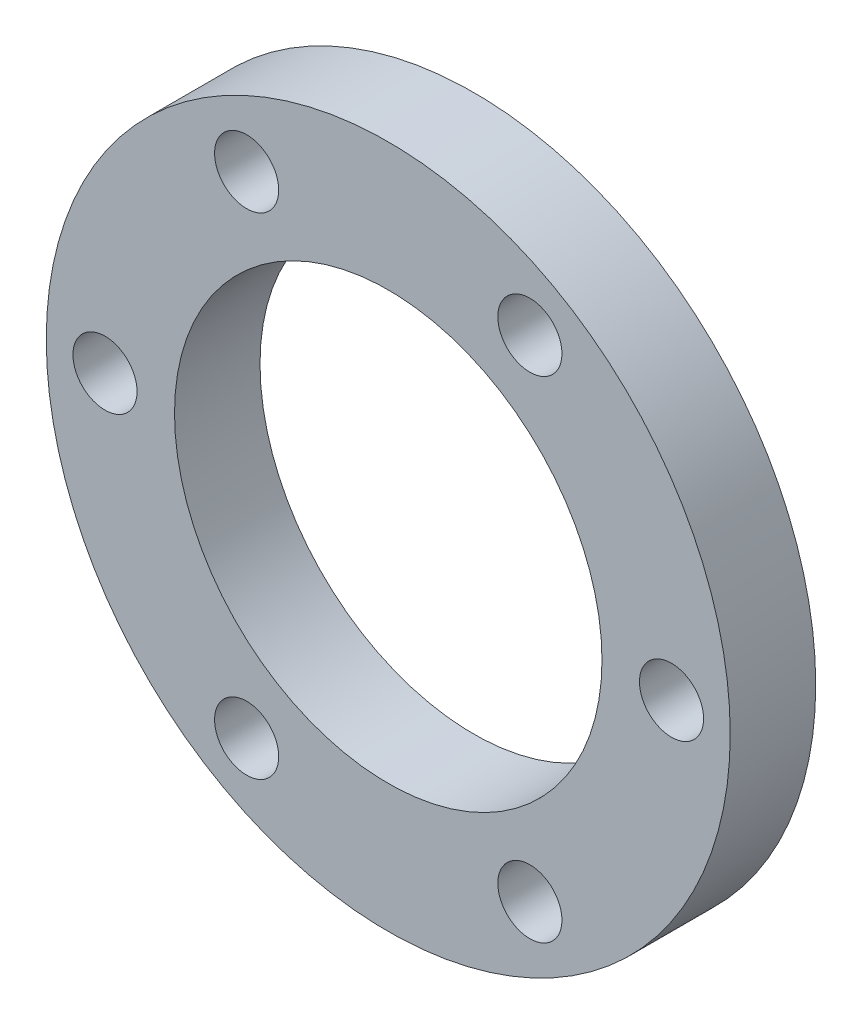
SolidWorks part; units mm, degrees
ref_plane "Front Plane" through (0, 0, 0) normal (0, 0, 1) x (1, 0, 0)
ref_plane "Top Plane" through (0, 0, 0) normal (0, 1, 0) x (1, 0, 0)
ref_plane "Right Plane" through (0, 0, 0) normal (1, 0, 0) x (0, 0, -1)
sketch "Sketch2" plane through (0, 0, 0) normal (0, 0, 1) x (1, 0, 0)
  line L0 (-99.7108, 0.0135) -> (108.6604, 0.0135) construction
  line L1 (0, 0) -> (-66.2605, 0) construction
  line L2 (0, 0) -> (-33.1303, 57.3833) construction
  circle A0 centre (0, 0) radius 80
  circle A1 centre (0, 0) radius 50
  circle A2 centre (0, 0) radius 66.2605
  circle A4 centre (-66.2605, 0) radius 7.5
  circle A5 centre (-33.1303, 57.3833) radius 7.5
  circle A6 centre (33.1303, 57.3833) radius 7.5
  circle A7 centre (66.2605, 0) radius 7.5
  circle A8 centre (33.1303, -57.3833) radius 7.5
  circle A9 centre (-33.1303, -57.3833) radius 7.5
  dimension "D1" = 160
  dimension "D2" = 132.521
  dimension "D3" = 15
  dimension "D4" = 100
  dimension "D5" = 6
  dimension "D6" = 60
extrude "Boss-Extrude3" add sketch "Sketch2" along normal blind 20 contours A0 A9 A2 A4 A5 A6 A7 A8 | A9 A2 A8 A7 A6 A5 A4 A1
